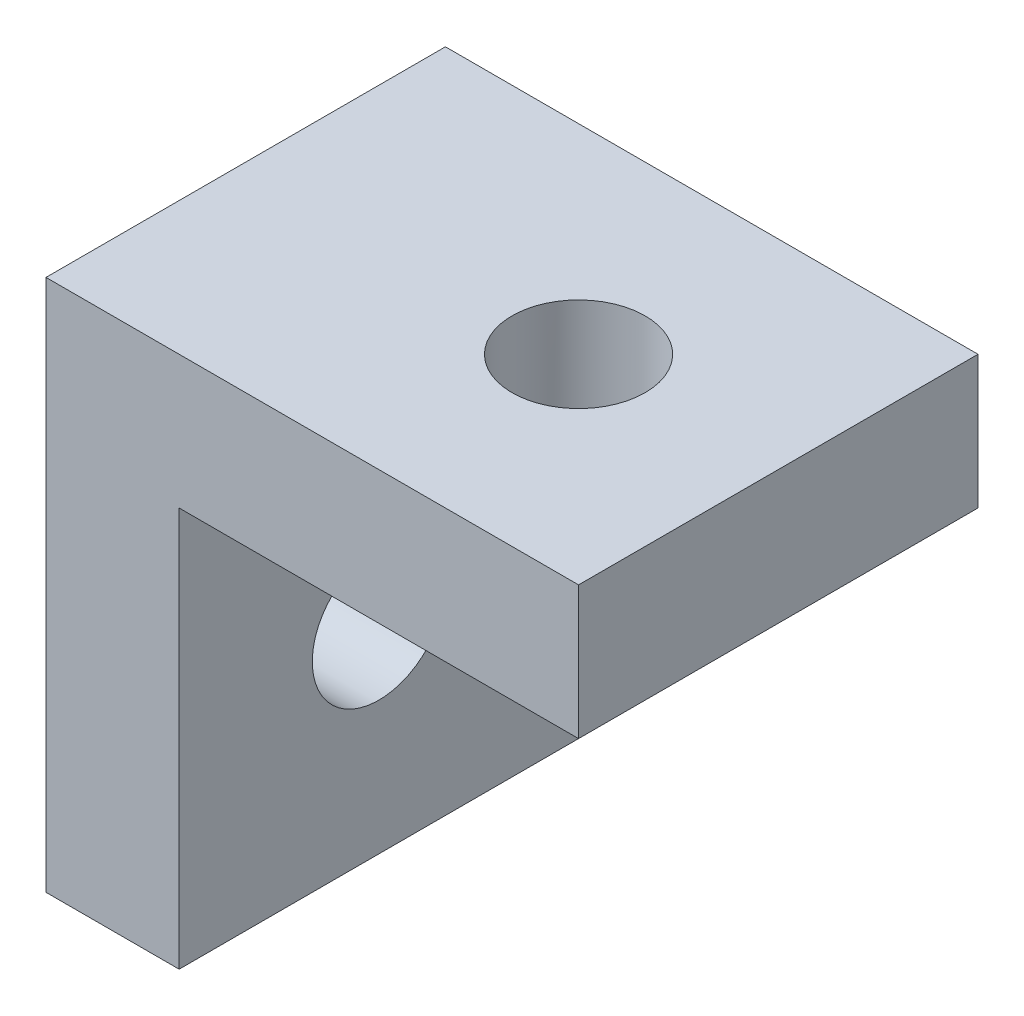
SolidWorks part; units mm, degrees
ref_plane "Front Plane" through (0, 0, 0) normal (0, 0, 1) x (1, 0, 0)
ref_plane "Top Plane" through (0, 0, 0) normal (0, 1, 0) x (1, 0, 0)
ref_plane "Right Plane" through (0, 0, 0) normal (1, 0, 0) x (0, 0, -1)
sketch "Sketch1" plane through (0, 0, 0) normal (0, 0, 1) x (1, 0, 0)
  line L1 (0, 0) -> (0, 30)
  line L2 (0, 30) -> (30, 30)
  dimension "D2" = 30
  dimension "D3" = 30
extrude "Extrude-Thin1" add sketch "Sketch1" along normal blind 30 thin thin type one direction reverse wall 10
sketch "Sketch2" plane through (0, 30, 0) normal (0, -1, 0) x (-1, 0, 0)
  line L0 (-30, -15) -> (-15, -15) construction
  line L1 (-30, -30) -> (-30, 0) construction
  circle A1 centre (-15, -15) radius 5
  dimension "D2" = 10
  dimension "D1" = 15
extrude "Cut-Extrude1" cut sketch "Sketch2" against normal through all both and the other way through all
sketch "Sketch3" plane through (0, 0, 0) normal (1, 0, 0) x (0, 0, -1)
  line L0 (-15, 30) -> (-15, 0) construction
  line L1 (-30, 30) -> (0, 30) construction
  line L3 (-30, 0) -> (0, 0) construction
  circle A0 centre (-15, 15) radius 5
  dimension "D1" = 10
extrude "Cut-Extrude2" cut sketch "Sketch3" against normal through all
